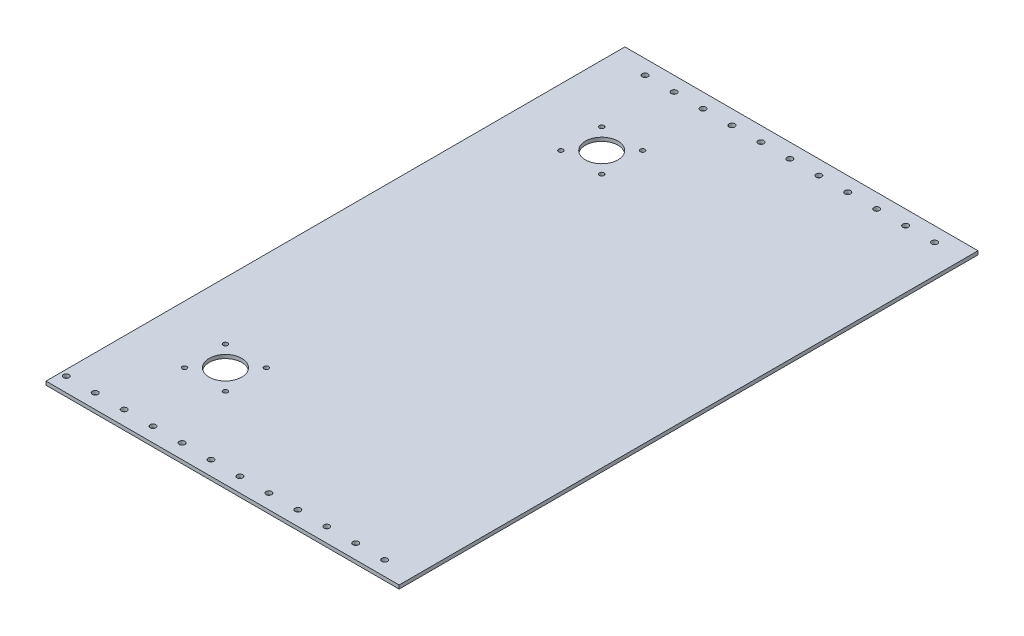
SolidWorks part; units mm, degrees
material "Lexan"
ref_plane "Front Plane" through (0, 0, 0) normal (0, 0, 1) x (1, 0, 0)
ref_plane "Top Plane" through (0, 0, 0) normal (0, 1, 0) x (1, 0, 0)
ref_plane "Right Plane" through (0, 0, 0) normal (1, 0, 0) x (0, 0, -1)
sketch "Sketch1" plane through (0, 0, 0) normal (0, 1, 0) x (1, 0, 0)
  line L1 (0, 0) -> (406.4, 0)
  line L2 (0, 0) -> (0, 508)
  line L3 (0, 508) -> (406.4, 508)
  line L4 (406.4, 0) -> (406.4, 508)
  dimension "D1" = 406.4
  dimension "D2" = 508
extrude "Boss-Extrude1" add sketch "Sketch1" along normal blind 3.175
sketch "Sketch2" plane through (0, 3.175, 0) normal (0, 1, 0) x (1, 0, 0)
  line L0 (107.95, 419.1) -> (107.95, 508) construction
  line L1 (50.8, 419.1) -> (165.1, 419.1) construction
  line L2 (406.4, 0) -> (406.4, 508) construction
  line L3 (50.8, 88.9) -> (165.1, 88.9) construction
  line L5 (406.4, 508) -> (0, 508) construction
  line L6 (107.95, 88.9) -> (107.95, 0) construction
  line L7 (0, 0) -> (406.4, 0) construction
  circle A0 centre (50.8, 419.1) radius 14.2875
  circle A1 centre (165.1, 419.1) radius 14.2875
  circle A2 centre (50.8, 88.9) radius 14.2875
  circle A3 centre (165.1, 88.9) radius 14.2875
  dimension "D1" = 28.575
  dimension "D2" = 28.575
  dimension "D3" = 28.575
  dimension "D4" = 28.575
  dimension "D5" = 114.3
  dimension "D6" = 114.3
  dimension "D7" = 330.2
  dimension "D9" = 241.3
extrude "Cut-Extrude1" cut sketch "Sketch2" against normal blind 3.175
sketch "Sketch3" plane through (0, 3.175, 0) normal (0, 1, 0) x (1, 0, 0)
  line L0 (0, 12.7) -> (406.4, 12.7) construction
  line L1 (0, 508) -> (0, 0) construction
  line L2 (406.4, 0) -> (406.4, 508) construction
  line L3 (0, 0) -> (406.4, 0) construction
  line L4 (101.6, 0) -> (101.6, 12.7) construction
  line L5 (0, 254) -> (406.4, 254) construction
  line L6 (101.6, 508) -> (101.6, 495.3) construction
  line L7 (0, 495.3) -> (406.4, 495.3) construction
  circle A0 centre (38.1, 12.7) radius 2.4892
  circle A1 centre (63.5, 12.7) radius 2.4892
  circle A2 centre (127, 12.7) radius 2.4892
  circle A3 centre (152.4, 12.7) radius 2.4892
  circle A4 centre (177.8, 12.7) radius 2.4892
  circle A5 centre (203.2, 12.7) radius 2.4892
  circle A6 centre (228.6, 12.7) radius 2.4892
  circle A7 centre (254, 12.7) radius 2.4892
  circle A8 centre (279.4, 12.7) radius 2.4892
  circle A9 centre (304.8, 12.7) radius 2.4892
  circle A10 centre (330.2, 12.7) radius 2.4892
  circle A11 centre (355.6, 12.7) radius 2.4892
  circle A12 centre (381, 12.7) radius 2.4892
  circle A13 centre (381, 495.3) radius 2.4892
  circle A14 centre (355.6, 495.3) radius 2.4892
  circle A15 centre (330.2, 495.3) radius 2.4892
  circle A16 centre (304.8, 495.3) radius 2.4892
  circle A17 centre (279.4, 495.3) radius 2.4892
  circle A18 centre (254, 495.3) radius 2.4892
  circle A19 centre (228.6, 495.3) radius 2.4892
  circle A20 centre (203.2, 495.3) radius 2.4892
  circle A21 centre (177.8, 495.3) radius 2.4892
  circle A22 centre (152.4, 495.3) radius 2.4892
  circle A23 centre (127, 495.3) radius 2.4892
  circle A24 centre (63.5, 495.3) radius 2.4892
  circle A25 centre (38.1, 495.3) radius 2.4892
  circle A27 centre (101.6, 12.7) radius 2.4892
  dimension "D1" = 4.9784
  dimension "D2" = 38.1
  dimension "D4" = 25.4
  dimension "D6" = 25.4
  dimension "D7" = 11
  dimension "D3" = 12.7
  dimension "D5" = 38.1
extrude "Cut-Extrude2" cut sketch "Sketch3" against normal through all both and the other way through all
sketch "Sketch4" plane through (0, 3.175, 0) normal (0, 1, 0) x (1, 0, 0)
  line L0 (25.4, 419.1) -> (38.1, 441.097) construction
  line L1 (38.1, 441.097) -> (63.5, 441.097) construction
  line L2 (63.5, 441.097) -> (76.2, 419.1) construction
  line L3 (76.2, 419.1) -> (63.5, 397.103) construction
  line L4 (63.5, 397.103) -> (38.1, 397.103) construction
  line L5 (38.1, 397.103) -> (25.4, 419.1) construction
  line L6 (0, 254) -> (406.4, 254) construction
  line L7 (183.0605, 401.1395) -> (147.1395, 401.1395) construction
  line L8 (183.0605, 401.1395) -> (183.0605, 437.0605) construction
  line L9 (183.0605, 437.0605) -> (147.1395, 437.0605) construction
  line L10 (147.1395, 401.1395) -> (147.1395, 437.0605) construction
  line L11 (183.0605, 401.1395) -> (147.1395, 437.0605) construction
  line L12 (183.0605, 437.0605) -> (147.1395, 401.1395) construction
  line L13 (0, 508) -> (0, 0) construction
  line L14 (406.4, 0) -> (406.4, 508) construction
  line L15 (183.0605, 70.9395) -> (147.1395, 106.8605) construction
  line L16 (183.0605, 106.8605) -> (147.1395, 70.9395) construction
  line L17 (147.1395, 106.8605) -> (147.1395, 70.9395) construction
  line L18 (183.0605, 70.9395) -> (147.1395, 70.9395) construction
  line L19 (183.0605, 106.8605) -> (183.0605, 70.9395) construction
  line L20 (183.0605, 106.8605) -> (147.1395, 106.8605) construction
  line L21 (38.1, 110.897) -> (25.4, 88.9) construction
  line L22 (63.5, 110.897) -> (38.1, 110.897) construction
  line L23 (76.2, 88.9) -> (63.5, 110.897) construction
  line L24 (63.5, 66.903) -> (76.2, 88.9) construction
  line L25 (38.1, 66.903) -> (63.5, 66.903) construction
  line L26 (25.4, 88.9) -> (38.1, 66.903) construction
  circle A0 centre (50.8, 419.1) radius 25.4 construction
  circle A1 centre (76.2, 419.1) radius 2.0193
  circle A2 centre (25.4, 419.1) radius 2.0193
  circle A3 centre (38.1, 441.097) radius 2.0193
  circle A4 centre (63.5, 441.097) radius 2.0193
  circle A5 centre (63.5, 397.103) radius 2.0193
  circle A6 centre (38.1, 397.103) radius 2.0193
  circle A7 centre (147.1395, 437.0605) radius 2.0193
  circle A8 centre (183.0605, 437.0605) radius 2.0193
  circle A9 centre (183.0605, 401.1395) radius 2.0193
  circle A10 centre (147.1395, 401.1395) radius 2.0193
  circle A11 centre (50.8, 88.9) radius 25.4 construction
  circle A12 centre (147.1395, 106.8605) radius 2.0193
  circle A13 centre (183.0605, 106.8605) radius 2.0193
  circle A14 centre (183.0605, 70.9395) radius 2.0193
  circle A15 centre (147.1395, 70.9395) radius 2.0193
  circle A16 centre (38.1, 110.897) radius 2.0193
  circle A17 centre (63.5, 110.897) radius 2.0193
  circle A18 centre (63.5, 66.903) radius 2.0193
  circle A19 centre (38.1, 66.903) radius 2.0193
  circle A20 centre (25.4, 88.9) radius 2.0193
  circle A21 centre (76.2, 88.9) radius 2.0193
  point P15 (165.1, 419.1)
  point P53 (165.1, 88.9)
  dimension "D1" = 50.8
  dimension "D2" = 4.0386
  dimension "D5" = 4.0386
  dimension "D3" = 35.921
  dimension "D4" = 35.921
extrude "Cut-Extrude3" cut sketch "Sketch4" against normal through all both and the other way through all
sketch "Sketch5" plane through (0, 0, 0) normal (-1, 0, 0) x (0, 0, 1)
  line L1 (-508, 3.175) -> (0, 3.175)
  line L2 (-508, 3.175) -> (-508, 0)
  line L3 (-508, 0) -> (0, 0)
  line L4 (0, 3.175) -> (0, 0)
extrude "Cut-Extrude4" cut sketch "Sketch5" against normal blind 96.52
